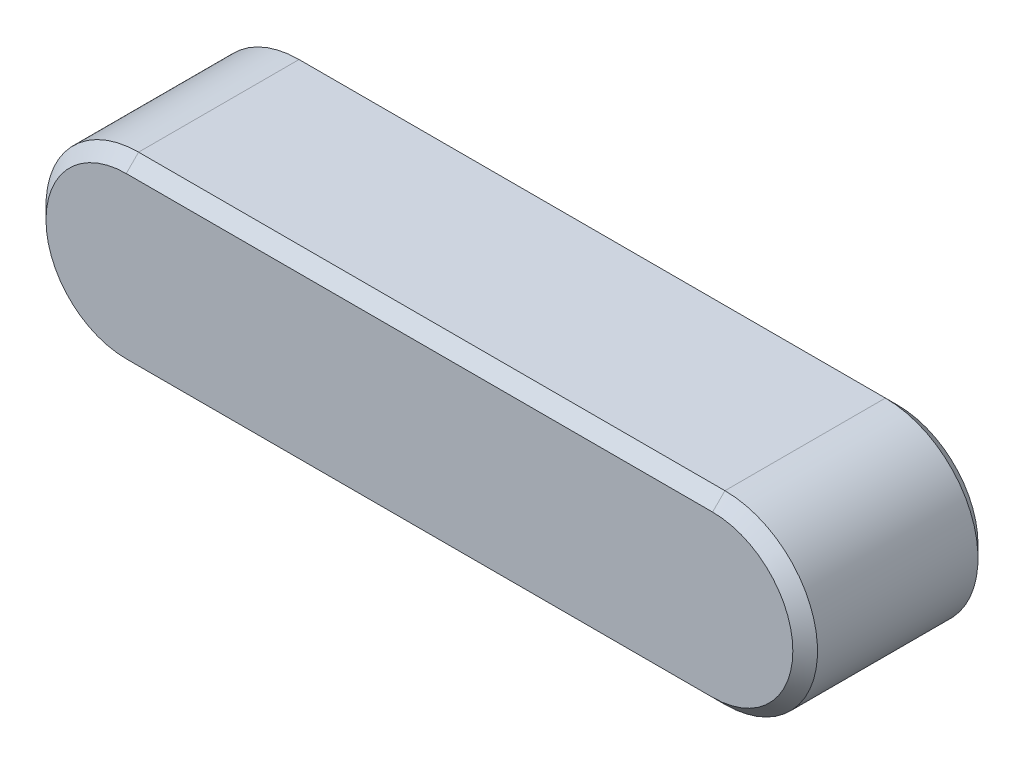
SolidWorks part; units mm, degrees
ref_plane "Front" through (0, 0, 0) normal (0, 0, 1) x (1, 0, 0)
ref_plane "Top" through (0, 0, 0) normal (0, 1, 0) x (1, 0, 0)
ref_plane "Right" through (0, 0, 0) normal (1, 0, 0) x (0, 0, -1)
sketch "Sketch1" plane through (0, 0, 0) normal (0, 0, 1) x (1, 0, 0)
  line L0 (-19, 3) -> (0, 3)
  line L1 (0, -3) -> (-19, -3)
  arc A0 (0, 3) -> (0, -3) centre (0, 0) cw
  arc A1 (-19, -3) -> (-19, 3) centre (-19, 0) cw
  dimension "L" = 25
  dimension "b" = 6
extrude "BaseKey" add sketch "Sketch1" along normal mid plane 6
sketch "Sketch2" plane through (0, 0, 0) normal (0, 0, 1) x (1, 0, 0)
  line L1 (-22, 3) -> (3, 3)
  line L2 (-22, 3) -> (-22, -3)
  line L3 (-22, -3) -> (3, -3)
  line L4 (3, 3) -> (3, -3)
  line L6 (0, -3) -> (-19, -3) construction
  line L7 (-19, 3) -> (0, 3) construction
  arc A2 (0, -3) -> (0, 3) centre (0, 0) ccw construction
  arc A3 (-19, 3) -> (-19, -3) centre (-19, 0) ccw construction
extrude "Extrude1" [suppressed] add sketch "Sketch2" along normal mid plane 6
sketch "Sketch3" plane through (0, 0, 0) normal (0, 0, 1) x (1, 0, 0)
  line L0 (3, 3) -> (-19, 3)
  line L1 (-19, -3) -> (3, -3)
  line L2 (3, -3) -> (3, 3)
  line L5 (-19, 3) -> (0, 3) construction
  arc A0 (-19, 3) -> (-19, -3) centre (-19, 0) ccw
  arc A1 (0, -3) -> (0, 3) centre (0, 0) ccw construction
  arc A4 (-19, 3) -> (-19, -3) centre (-19, 0) ccw construction
extrude "Extrude2" [suppressed] add sketch "Sketch3" along normal mid plane 6
chamfer "Chamfer1" distance 0.4 angle 45 8 edges at (3, 0, -3) (-9.5, -3, -3) (-22, 0, -3) (-9.5, 3, -3) (-22, 0, 3) (-9.5, -3, 3) (3, 0, 3) (-9.5, 3, 3)
equation "\"D1@Extrude1\"=\"h@BaseKey\""
equation "\"D1@Extrude2\"=\"h@BaseKey\""
